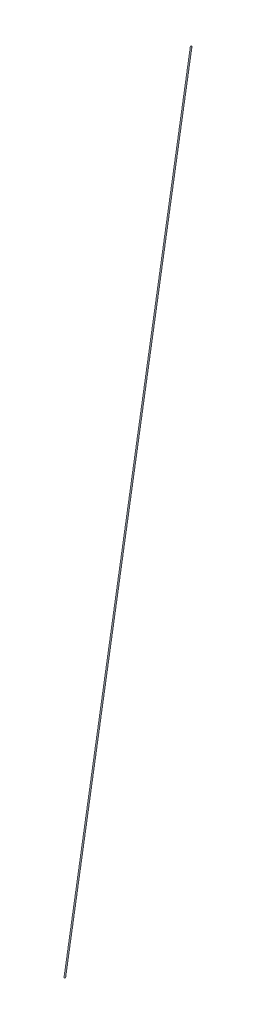
SolidWorks part; units mm, degrees
ref_plane "前视基准面" through (0, 0, 0) normal (0, 0, 1) x (1, 0, 0)
ref_plane "上视基准面" through (0, 0, 0) normal (0, 1, 0) x (1, 0, 0)
ref_plane "右视基准面" through (0, 0, 0) normal (1, 0, 0) x (0, 0, -1)
sketch "草图1" plane through (0, 0, 0) normal (0, 1, 0) x (1, 0, 0)
  line L0 (0, 0) -> (0, 217.5)
sketch "草图2" plane through (0, 0, 0) normal (0, 0, 1) x (1, 0, 0)
  line L0 (0, 0) -> (0, 1279.38)
sketch "草图3" plane through (0, 0, 0) normal (1, 0, 0) x (0, 0, -1)
  line L0 (217.5, 0) -> (0, 1279.38)
  line L1 (0, 0) -> (217.5, 0) construction
  line L2 (0, 0) -> (0, 1279.38) construction
  line L3 (0, 1279.38) -> (19.7171, 1282.732)
ref_plane "基准面1" through (0, 1243.4427, 211.3905) normal (0, 0.9859, 0.1676) x (1, 0, 0)
sketch "草图4" plane through (0, 1243.4427, 211.3905) normal (0, 0.9859, 0.1676) x (1, 0, 0)
  circle A0 centre (0, 214.4235) radius 1
ref_plane "基准面2" through (0, 0, -217.5) normal (0, 0, 1) x (1, 0, 0)
sketch "草图5" plane through (0, 0, 0) normal (1, 0, 0) x (0, 0, -1)
  line L0 (0, 1279.38) -> (217.5, 1279.38)
  line L1 (217.5, 1.1) -> (217.5, -1.1) construction
  line L2 (217.5, 1279.38) -> (217.5, 0)
  line L3 (217.5, 0) -> (0, 0)
  line L4 (0, 0) -> (217.5, 1279.38)
  line L5 (217.5, 1279.38) -> (197.7829, 1282.732)
ref_plane "基准面3" through (0, 1279.38, -217.5) normal (0, 0.9859, -0.1676) x (1, 0, 0)
sketch "草图6" plane through (0, 1279.38, -217.5) normal (0, 0.9859, -0.1676) x (1, 0, 0)
  circle A0 centre (0, 0) radius 1
sweep "扫描1" add profiles "草图6" path "草图5"
